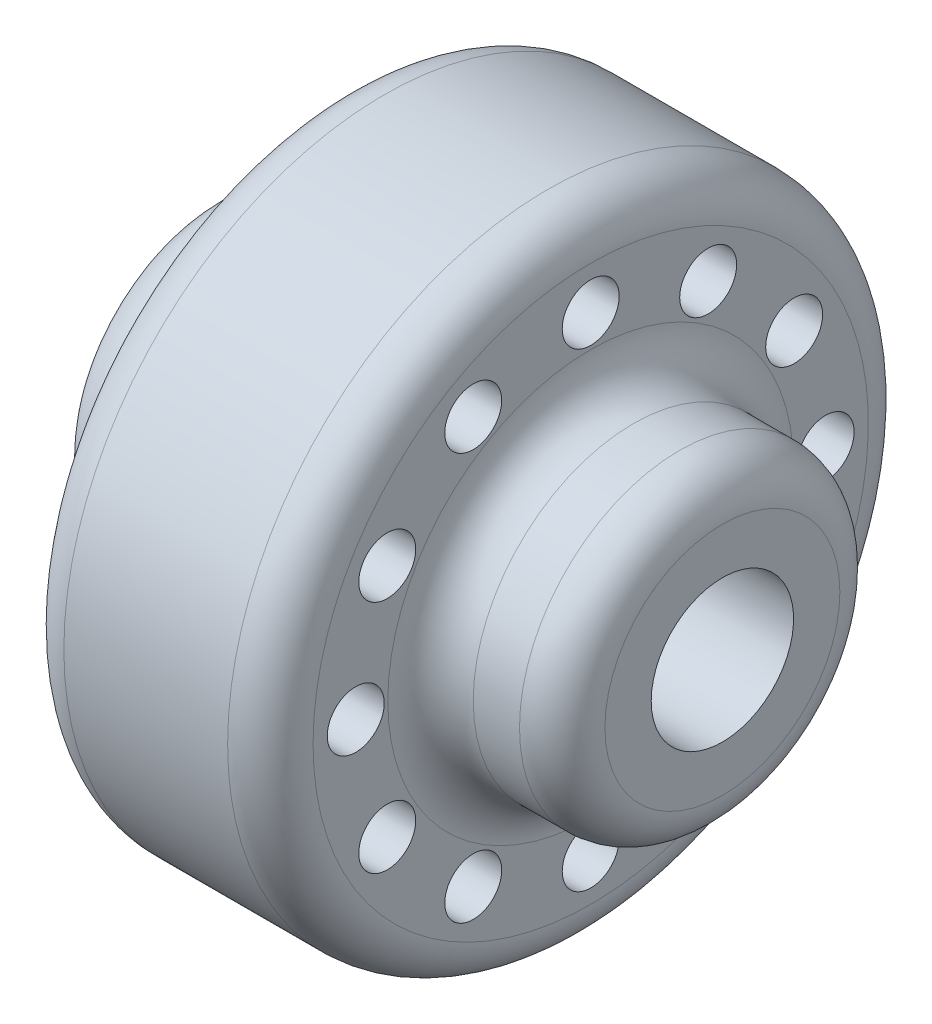
SolidWorks part; units mm, degrees
ref_plane "Front Plane" through (0, 0, 0) normal (0, 0, 1) x (1, 0, 0)
ref_plane "Top Plane" through (0, 0, 0) normal (0, 1, 0) x (1, 0, 0)
ref_plane "Right Plane" through (0, 0, 0) normal (1, 0, 0) x (0, 0, -1)
sketch "Sketch1" plane through (0, 0, 0) normal (0, 0, 1) x (1, 0, 0)
  line L1 (14.5, 22.5) -> (3, 22.5)
  line L2 (0, 19.5) -> (0, 14.25)
  line L3 (-3, 11.25) -> (-6.25, 11.25)
  line L4 (-9.25, 8.25) -> (-9.25, 0)
  line L5 (-9.25, 0) -> (26.75, 0)
  line L6 (26.75, 8.25) -> (26.75, 0)
  line L7 (20.5, 11.25) -> (23.75, 11.25)
  line L8 (17.5, 19.5) -> (17.5, 14.25)
  line L9 (25, 0) -> (87.15, 0) construction
  arc A0 (0, 14.25) -> (-3, 11.25) centre (-3, 14.25) cw
  arc A1 (20.5, 11.25) -> (17.5, 14.25) centre (20.5, 14.25) cw
  arc A2 (-6.25, 11.25) -> (-9.25, 8.25) centre (-6.25, 8.25) ccw
  arc A3 (26.75, 8.25) -> (23.75, 11.25) centre (23.75, 8.25) ccw
  arc A4 (3, 22.5) -> (0, 19.5) centre (3, 19.5) ccw
  arc A5 (17.5, 19.5) -> (14.5, 22.5) centre (14.5, 19.5) ccw
  point P18 (0, 11.25)
  point P21 (17.5, 11.25)
  point P24 (-9.25, 11.25)
  point P27 (26.75, 11.25)
  point P30 (0, 22.5)
  point P33 (17.5, 22.5)
  dimension "D4" = 3
  dimension "D1" = 17.5
  dimension "D2" = 11.25
  dimension "D3" = 22.5
  dimension "D5" = 11.25
other "AlignGroup2"
revolve "Revolve1" add sketch "Sketch1" angle 360 about L9
sketch "Sketch2" plane through (-9.25, 0, 0) normal (-1, 0, 0) x (0, 0, 1)
  circle A0 centre (0, 0) radius 5
extrude "Cut-Extrude1" cut sketch "Sketch2" against normal through all
sketch "Sketch3" plane through (0, 0, 0) normal (-1, 0, 0) x (0, 0, 1)
  circle A0 centre (0, 16.5) radius 2
  dimension "D2" = 4
  dimension "D1" = 16.5
extrude "Cut-Extrude2" cut sketch "Sketch3" against normal through all
pattern_circular "CirPattern1" count 12 over 360 about axis through (0, 0, 0) along (1, 0, 0) of "Cut-Extrude2"
